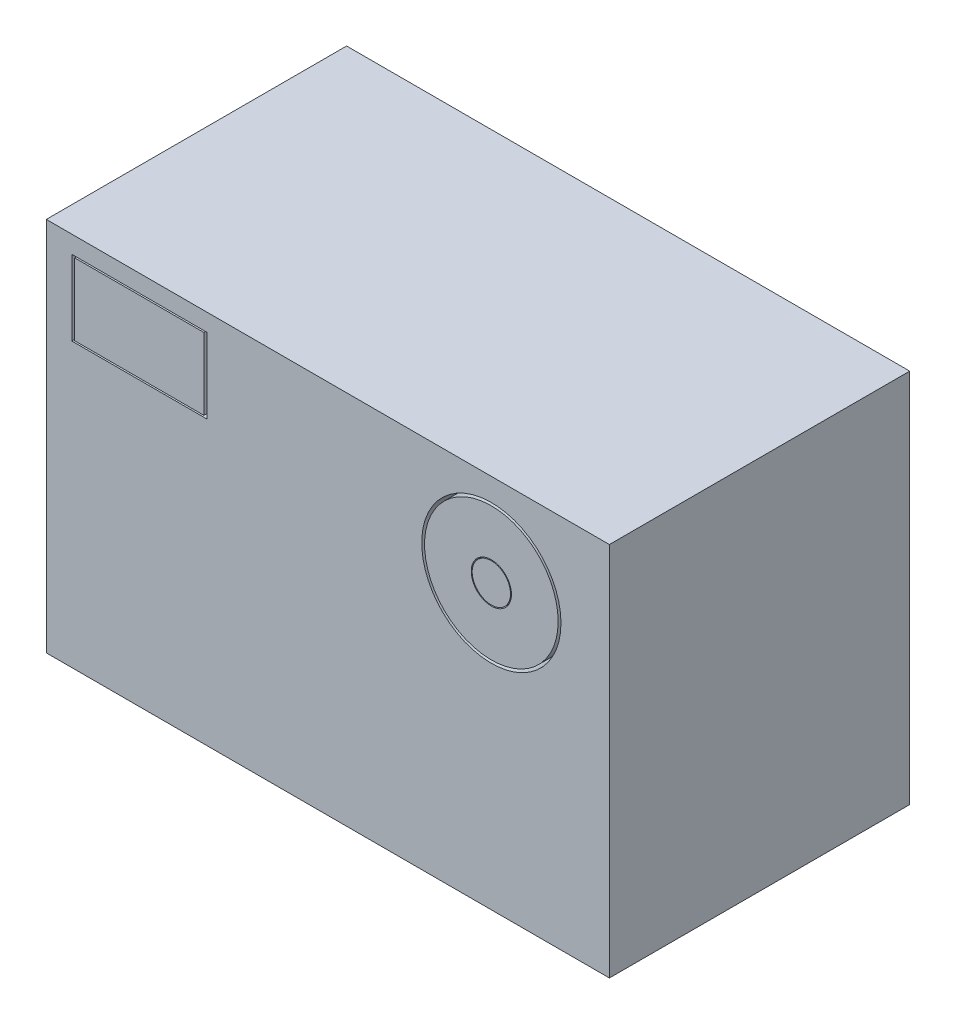
SolidWorks part; units mm, degrees
ref_plane "Front Plane" through (0, 0, 0) normal (0, 0, 1) x (1, 0, 0)
ref_plane "Top Plane" through (0, 0, 0) normal (0, 1, 0) x (1, 0, 0)
ref_plane "Right Plane" through (0, 0, 0) normal (1, 0, 0) x (0, 0, -1)
sketch "Sketch1" plane through (0, 0, 0) normal (0, 0, 1) x (1, 0, 0)
  line L1 (-37.5, 25) -> (37.5, 25)
  line L2 (-37.5, 25) -> (-37.5, -25)
  line L3 (-37.5, -25) -> (37.5, -25)
  line L4 (37.5, 25) -> (37.5, -25)
  line L5 (-37.5, 25) -> (37.5, -25) construction
  line L6 (-37.5, -25) -> (37.5, 25) construction
  point P0 (0, 0)
  dimension "D1" = 75
  dimension "D2" = 50
extrude "Boss-Extrude1" add sketch "Sketch1" along normal blind 40
sketch "Sketch2" plane through (0, 0, 40) normal (0, 0, 1) x (1, 0, 0)
  circle A0 centre (21.7782, 12.7141) radius 9.273
extrude "Cut-Extrude1" cut sketch "Sketch2" against normal blind 14
sketch "Sketch3" plane through (0, 0, 26) normal (0, 0, 1) x (1, 0, 0)
  circle A0 centre (21.7782, 12.7141) radius 8.8957
  circle A1 centre (21.7782, 12.7141) radius 2.6766
extrude "Boss-Extrude2" add sketch "Sketch3" along normal blind 14
sketch "Sketch4" plane through (0, 0, 26) normal (0, 0, 1) x (1, 0, 0)
  circle A0 centre (21.7782, 12.7141) radius 2.5529
extrude "Boss-Extrude3" add sketch "Sketch4" along normal blind 14
sketch "Sketch5" plane through (0, 0, 40) normal (0, 0, 1) x (1, 0, 0)
  line L5 (-34.1069, 12.6744) -> (-16.1069, 12.6744)
  line L6 (-34.1069, 12.6744) -> (-34.1069, 22.6744)
  line L11 (-34.1069, 22.6744) -> (-16.1069, 22.6744)
  line L12 (-16.1069, 12.6744) -> (-16.1069, 22.6744)
  line L13 (-34.1069, 12.6744) -> (-16.1069, 22.6744) construction
  line L14 (-34.1069, 22.6744) -> (-16.1069, 12.6744) construction
  line L15 (-33.7128, 12.8933) -> (-16.5011, 12.8933)
  line L16 (-33.7128, 12.8933) -> (-33.7128, 22.4554)
  line L17 (-33.7128, 22.4554) -> (-16.5011, 22.4554)
  line L18 (-16.5011, 12.8933) -> (-16.5011, 22.4554)
  line L19 (-33.7128, 12.8933) -> (-16.5011, 22.4554) construction
  line L20 (-33.7128, 22.4554) -> (-16.5011, 12.8933) construction
  point P0 (-25.1069, 17.6744)
  point P1 (-25.1069, 17.6744)
  point P6 (-25.1069, 17.6744)
  dimension "D1" = 18
  dimension "D2" = 10
extrude "Cut-Extrude2" cut sketch "Sketch5" against normal blind 7
sketch "Sketch6" plane through (0, -25, 0) normal (0, -1, 0) x (1, 0, 0)
  line L0 (-37.5, 40) -> (37.5, 0) construction
  circle A0 centre (0, 20) radius 5
  dimension "D1" = 10
extrude "Cut-Extrude3" cut sketch "Sketch6" against normal blind 10
